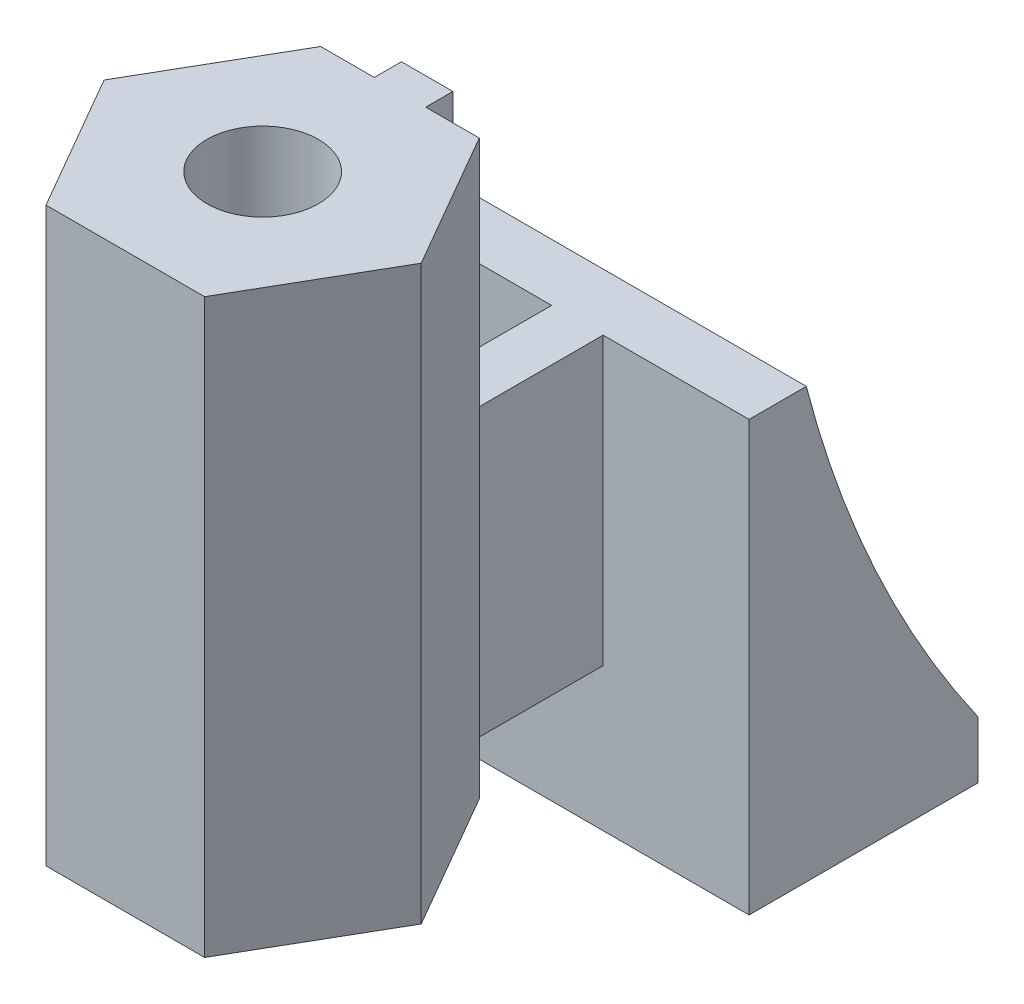
SolidWorks part; units mm, degrees
ref_plane "Front Plane" through (0, 0, 0) normal (0, 0, 1) x (1, 0, 0)
ref_plane "Top Plane" through (0, 0, 0) normal (0, 1, 0) x (1, 0, 0)
ref_plane "Right Plane" through (0, 0, 0) normal (1, 0, 0) x (0, 0, -1)
sketch "Sketch2" plane through (0, 0, 0) normal (0, 1, 0) x (1, 0, 0)
  line L0 (0, 0) -> (0, 5) construction
  line L1 (5.5426, 0) -> (2.7713, 4.8)
  line L2 (2.7713, 4.8) -> (0.9, 4.8)
  line L3 (-2.7713, 4.8) -> (-5.5426, 0)
  line L4 (-5.5426, 0) -> (-2.7713, -4.8)
  line L5 (-2.7713, -4.8) -> (2.7713, -4.8)
  line L6 (2.7713, -4.8) -> (5.5426, 0)
  line L7 (-0.9, 4.8) -> (-0.9, 5.75)
  line L8 (-0.9, 5.75) -> (0.9, 5.75)
  line L9 (0, 5) -> (0, 5.75) construction
  line L10 (0.9, 4.8) -> (0.9, 5.75)
  line L11 (-0.9, 4.8) -> (-2.7713, 4.8)
  circle A0 centre (0, 0) radius 4.8 construction
  dimension "D1" = 9.6
  dimension "D2" = 0.95
  dimension "D3" = 0.9
extrude "Boss-Extrude1" add sketch "Sketch2" along normal blind 20
sketch "Sketch4" plane through (0, 0, 0) normal (0, -1, 0) x (-1, 0, 0)
  circle A0 centre (0, 0) radius 1.95
  dimension "D1" = 3.9
extrude "Cut-Extrude1" cut sketch "Sketch4" against normal up to surface (20 mm away) up to face at (0, 20, -2.11)
sketch "Sketch6" plane through (0, 0, 0) normal (0, -1, 0) x (1, 0, 0)
  line L0 (0.9, -5.75) -> (0.9, -11)
  line L1 (0.9, -5.75) -> (-0.9, -5.75) construction
  line L2 (0.9, -4.8) -> (0.9, -5.75) construction
  line L3 (0.9, -11) -> (6, -11)
  line L4 (6, -11) -> (6, -19)
  line L5 (6, -19) -> (-6, -19)
  line L6 (0, -19) -> (0, -5.75) construction
  line L7 (-6, -11) -> (-6, -19)
  line L8 (-0.9, -11) -> (-6, -11)
  line L9 (-0.9, -5.75) -> (-0.9, -11)
  line L10 (0.9, -5.75) -> (-0.9, -5.75)
  line L11 (0.9, -4.8) -> (-0.9, -4.8) construction
  dimension "D1" = 12
  dimension "D2" = 8
  dimension "D3" = 11
extrude "Boss-Extrude2" add sketch "Sketch6" against normal blind 10
sketch "Sketch8" plane through (0, 0, 0) normal (0, -1, 0) x (-1, 0, 0)
  line L1 (-6, 19) -> (6, 19)
  line L2 (-6, 19) -> (-6, 11)
  line L3 (-6, 11) -> (6, 11)
  line L4 (6, 19) -> (6, 11)
extrude "Boss-Extrude3" add sketch "Sketch8" along normal blind 5
sketch "Sketch9" plane through (6, 0, 0) normal (1, 0, 0) x (0, 0, -1)
  line L0 (19, 10) -> (11, 10) construction
  line L1 (19, 10) -> (19, -5) construction
  line L2 (13, 10) -> (19, 10)
  line L3 (19, 10) -> (19, -3)
  arc A0 (13, 10) -> (19, -3) centre (51.732, 19.9917) ccw
  dimension "D1" = 2
  dimension "D2" = 40
  dimension "D3" = 2
extrude "Cut-Extrude3" cut sketch "Sketch9" against normal up to next
